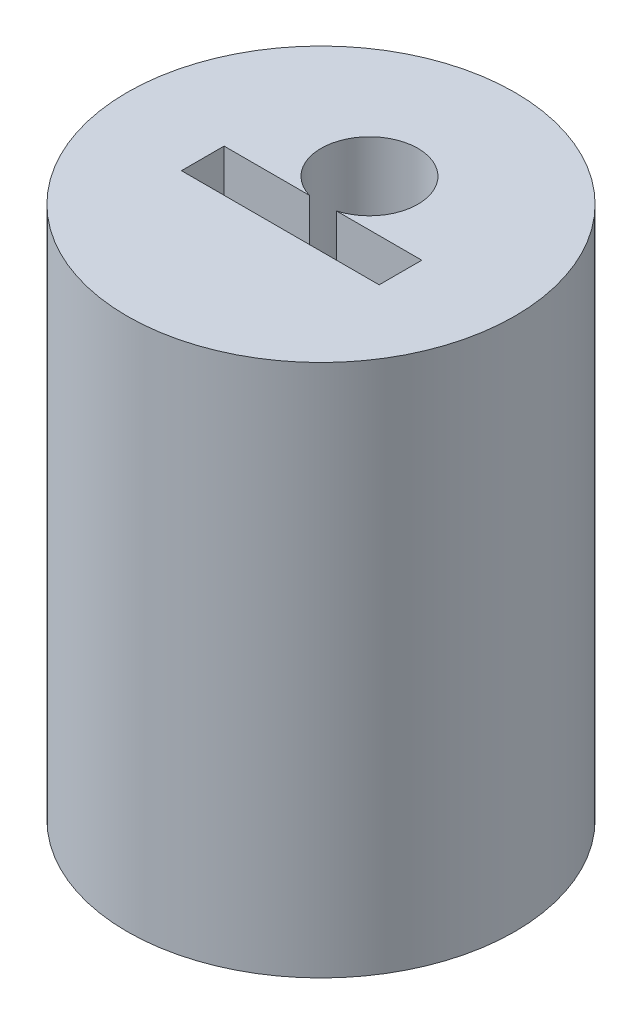
SolidWorks part; units mm, degrees
material "Ceramic Porcelain"
ref_plane "Front Plane" through (0, 0, 0) normal (0, 0, 1) x (1, 0, 0)
ref_plane "Top Plane" through (0, 0, 0) normal (0, 1, 0) x (1, 0, 0)
ref_plane "Right Plane" through (0, 0, 0) normal (1, 0, 0) x (0, 0, -1)
sketch "Sketch1" plane through (0, 0, 0) normal (0, 1, 0) x (1, 0, 0)
  line L0 (-0.51, -0.21) -> (0.51, -0.21)
  line L1 (0.51, -0.21) -> (0.51, 0.01)
  line L2 (-0.5, -0.2) -> (0.5, -0.2) construction
  line L3 (-0.5, -0.2) -> (-0.5, 0) construction
  line L4 (-0.5, 0) -> (0.5, 0) construction
  line L5 (0.5, -0.2) -> (0.5, 0) construction
  line L6 (-0.51, 0.01) -> (-0.07, 0.01)
  line L7 (-0.51, -0.21) -> (-0.51, 0.01)
  line L8 (0.07, 0.01) -> (0.51, 0.01)
  line L9 (-0.51, 0.01) -> (0.51, 0.01) construction
  circle A0 centre (0, 0) radius 1
  arc A1 (0.07, 0.01) -> (-0.07, 0.01) centre (0, 0.25) ccw
  point P4 (0, 0)
  dimension "D1" = 2
  dimension "D5" = 0.5
  dimension "D2" = 0.01
  dimension "D3" = 0.2
  dimension "D4" = 1
extrude "Boss-Extrude1" add sketch "Sketch1" along normal mid plane 2.5
sketch "Sketch3" plane through (0, -1.25, 0) normal (0, -1, 0) x (1, 0, 0)
  circle A0 centre (0, 0) radius 1 construction
  circle A1 centre (0, 0) radius 1
extrude "Boss-Extrude2" add sketch "Sketch3" along normal blind 0.25
